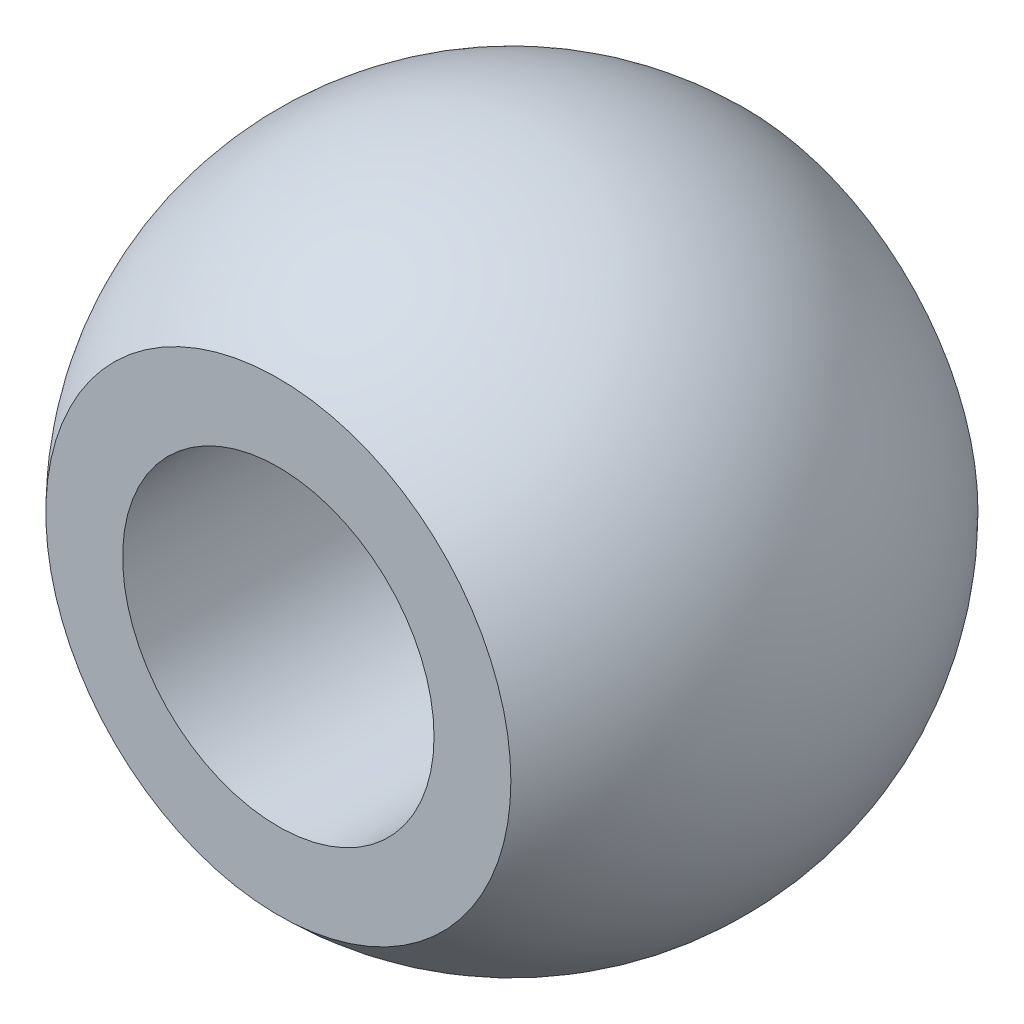
SolidWorks part; units mm, degrees
ref_plane "Front Plane" through (0, 0, 0) normal (0, 0, 1) x (1, 0, 0)
ref_plane "Top Plane" through (0, 0, 0) normal (0, 1, 0) x (1, 0, 0)
ref_plane "Right Plane" through (0, 0, 0) normal (1, 0, 0) x (0, 0, -1)
ref_plane "Plane1" through (0, 0, 0) normal (1, 0, 0) x (0, 0, -1)
sketch "Sketch1" plane through (0, 0, 0) normal (1, 0, 0) x (0, 0, -1)
  line L0 (-4.5, 3) -> (4.5, 3)
  line L1 (4.5, 3) -> (4.5, 4.4802)
  line L2 (-4.5, 4.4802) -> (-4.5, 3)
  line L3 (4.5, 0) -> (-4.5, 0) construction
  arc A0 (4.5, 4.4802) -> (-4.5, 4.4802) centre (0, 0) ccw
revolve "Revolve1" add sketch "Sketch1" angle 360 about L3
sketch "Sketch2" plane through (0, 0, 0) normal (0, 0, 1) x (1, 0, 0)
  point P0 (0, 0)
